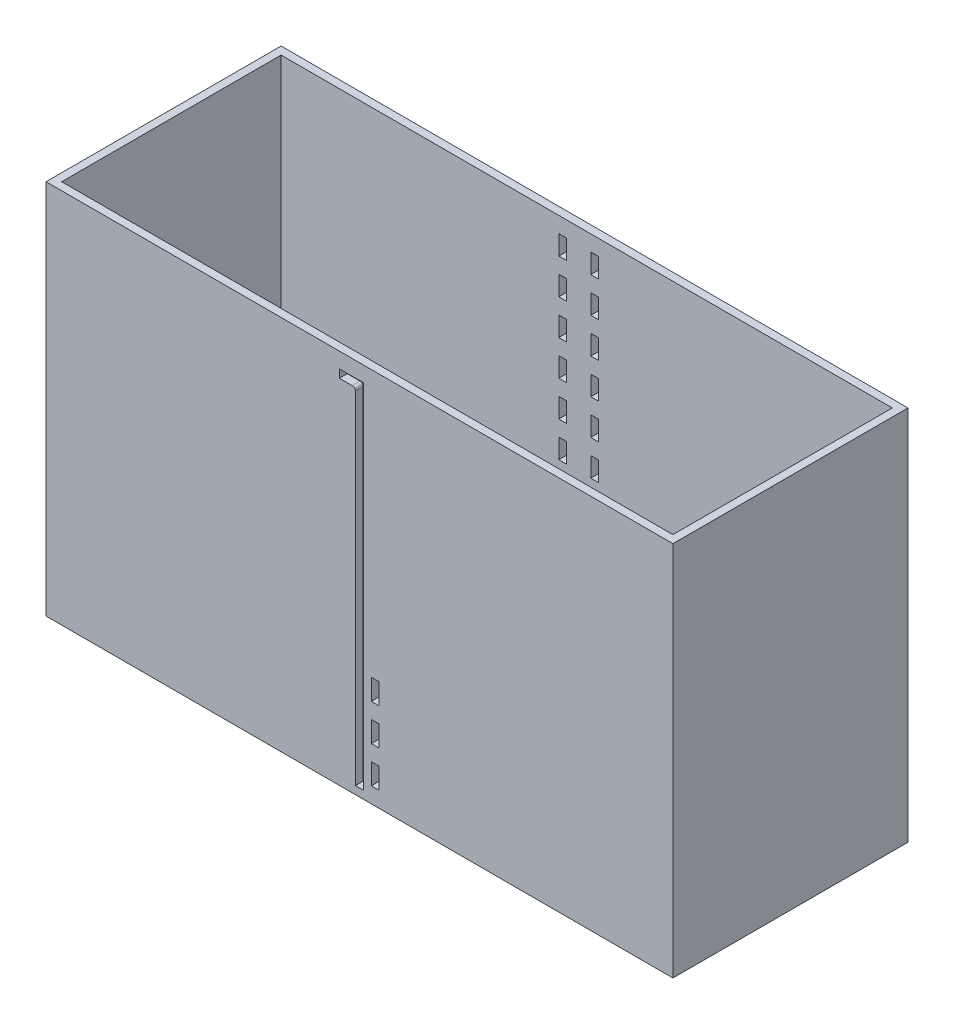
SolidWorks part; units mm, degrees
material "Acrylic (Medium-high impact)"
ref_plane "Front Plane" through (0, 0, 0) normal (0, 0, 1) x (1, 0, 0)
ref_plane "Top Plane" through (0, 0, 0) normal (0, 1, 0) x (1, 0, 0)
ref_plane "Right Plane" through (0, 0, 0) normal (1, 0, 0) x (0, 0, -1)
sketch "Sketch1" plane through (0, 0, 0) normal (0, 1, 0) x (1, 0, 0)
  line L1 (-254, 95.25) -> (254, 95.25)
  line L2 (-254, 95.25) -> (-254, -95.25)
  line L3 (-254, -95.25) -> (254, -95.25)
  line L4 (254, 95.25) -> (254, -95.25)
  point P4 (-254, 0)
  point P6 (0, 95.25)
  dimension "D1" = 190.5
  dimension "D2" = 508
extrude "Boss-Extrude1" add sketch "Sketch1" along normal blind 6.35
sketch "Sketch2" plane through (0, 6.35, 0) normal (0, 1, 0) x (1, 0, 0)
  line L0 (254, -95.25) -> (254, 95.25) construction
  line L1 (-254, 95.25) -> (254, 95.25)
  line L2 (-254, 95.25) -> (-254, -95.25)
  line L3 (-254, -95.25) -> (254, -95.25)
  line L4 (254, 95.25) -> (254, -95.25)
  line L5 (-254, -95.25) -> (254, -95.25) construction
  line L7 (-247.65, 88.9) -> (247.65, 88.9)
  line L8 (-247.65, 88.9) -> (-247.65, -88.9)
  line L9 (-247.65, -88.9) -> (247.65, -88.9)
  line L10 (247.65, 88.9) -> (247.65, -88.9)
  point P7 (-247.65, 0)
  point P14 (-254, 0)
  point P15 (0, -88.9)
  point P16 (0, -95.25)
  point P17 (247.65, 0)
  point P18 (254, 0)
  dimension "D1" = 6.35
  dimension "D2" = 6.35
extrude "Boss-Extrude2" add sketch "Sketch2" along normal blind 298.45
sketch "Sketch3" plane through (0, 0, 95.25) normal (0, 0, 1) x (1, 0, 0)
  line L0 (0, 304.8) -> (0, 0) construction
  line L1 (-254, 304.8) -> (254, 304.8) construction
  line L2 (-247.65, 6.35) -> (247.65, 6.35) construction
  line L4 (-3.302, 283.21) -> (-3.302, 6.35)
  line L5 (-3.302, 6.35) -> (3.302, 6.35)
  line L6 (3.302, 292.354) -> (3.302, 6.35)
  line L7 (3.302, 292.354) -> (-16.256, 292.354)
  line L9 (-5.842, 285.75) -> (-16.256, 285.75)
  line L10 (-16.256, 292.354) -> (-16.256, 285.75)
  line L11 (3.302, 101.6) -> (16.002, 101.6) construction
  line L12 (-254, 0) -> (254, 0) construction
  line L13 (12.827, 88.9) -> (12.827, 101.6) construction
  line L14 (9.652, 88.9) -> (16.002, 88.9)
  line L15 (9.652, 88.9) -> (9.652, 71.9667)
  line L16 (9.652, 71.9667) -> (16.002, 71.9667)
  line L17 (16.002, 88.9) -> (16.002, 71.9667)
  line L18 (9.652, 42.3333) -> (16.002, 42.3333)
  line L19 (9.652, 42.3333) -> (9.652, 59.2667)
  line L20 (9.652, 59.2667) -> (16.002, 59.2667)
  line L21 (16.002, 42.3333) -> (16.002, 59.2667)
  line L26 (9.652, 29.6333) -> (16.002, 29.6333)
  line L27 (9.652, 29.6333) -> (9.652, 12.7)
  line L28 (9.652, 12.7) -> (16.002, 12.7)
  line L29 (16.002, 29.6333) -> (16.002, 12.7)
  line L30 (12.827, 59.2667) -> (12.827, 71.9667) construction
  line L31 (12.827, 29.6333) -> (12.827, 42.3333) construction
  line L32 (12.827, 12.7) -> (12.827, 0) construction
  arc A0 (-3.302, 283.21) -> (-5.842, 285.75) centre (-5.842, 283.21) ccw
  point P5 (0, 6.35)
  dimension "D5" = 2.54
  dimension "D1" = 6.604
  dimension "D2" = 12.954
  dimension "D3" = 6.604
  dimension "D4" = 286.004
  dimension "D6" = 101.6
  dimension "D7" = 12.7
  dimension "D8" = 12.7
  dimension "D9" = 6.35
extrude "Cut-Extrude1" cut sketch "Sketch3" against normal blind 12.7
sketch "Sketch4" plane through (0, 0, -88.9) normal (0, 0, 1) x (1, 0, 0)
  line L0 (-254, 304.8) -> (254, 304.8) construction
  line L1 (-22.606, 304.8) -> (-16.256, 304.8)
  line L2 (-22.606, 304.8) -> (-22.606, 6.35)
  line L3 (-22.606, 6.35) -> (-16.256, 6.35)
  line L4 (-16.256, 304.8) -> (-16.256, 6.35)
  line L5 (6.477, 263.525) -> (6.477, 247.65) construction
  line L6 (-16.256, 292.354) -> (-16.256, 285.75) construction
  line L7 (3.302, 304.8) -> (9.652, 304.8)
  line L8 (3.302, 304.8) -> (3.302, 6.35)
  line L9 (3.302, 6.35) -> (9.652, 6.35)
  line L10 (9.652, 304.8) -> (9.652, 6.35)
  line L11 (247.65, 6.35) -> (-247.65, 6.35) construction
  line L12 (3.302, 6.35) -> (3.302, 292.354) construction
  line L13 (-16.256, 304.8) -> (-22.606, 304.8)
  line L14 (-16.256, 304.8) -> (-16.256, 292.1)
  line L15 (-16.256, 292.1) -> (-22.606, 292.1)
  line L16 (-22.606, 304.8) -> (-22.606, 292.1)
  line L17 (-16.256, 276.225) -> (-22.606, 276.225)
  line L18 (-16.256, 276.225) -> (-16.256, 263.525)
  line L19 (-16.256, 263.525) -> (-22.606, 263.525)
  line L20 (-22.606, 276.225) -> (-22.606, 263.525)
  line L21 (-22.606, 6.35) -> (-16.256, 6.35)
  line L22 (-22.606, 6.35) -> (-22.606, 19.05)
  line L23 (-22.606, 19.05) -> (-16.256, 19.05)
  line L24 (-16.256, 6.35) -> (-16.256, 19.05)
  line L25 (-22.606, 34.925) -> (-16.256, 34.925)
  line L26 (-22.606, 34.925) -> (-22.606, 47.625)
  line L27 (-22.606, 47.625) -> (-16.256, 47.625)
  line L28 (-16.256, 34.925) -> (-16.256, 47.625)
  line L29 (-22.606, 92.075) -> (-16.256, 92.075)
  line L30 (-22.606, 92.075) -> (-22.606, 104.775)
  line L31 (-22.606, 104.775) -> (-16.256, 104.775)
  line L32 (-16.256, 92.075) -> (-16.256, 104.775)
  line L33 (-22.606, 149.225) -> (-16.256, 149.225)
  line L34 (-22.606, 149.225) -> (-22.606, 161.925)
  line L35 (-22.606, 161.925) -> (-16.256, 161.925)
  line L36 (-16.256, 149.225) -> (-16.256, 161.925)
  line L37 (-22.606, 177.8) -> (-16.256, 177.8)
  line L38 (-22.606, 177.8) -> (-22.606, 190.5)
  line L39 (-22.606, 190.5) -> (-16.256, 190.5)
  line L40 (-16.256, 177.8) -> (-16.256, 190.5)
  line L41 (-22.606, 206.375) -> (-16.256, 206.375)
  line L42 (-22.606, 206.375) -> (-22.606, 219.075)
  line L43 (-22.606, 219.075) -> (-16.256, 219.075)
  line L44 (-16.256, 206.375) -> (-16.256, 219.075)
  line L45 (-22.606, 234.95) -> (-16.256, 234.95)
  line L46 (-22.606, 234.95) -> (-22.606, 247.65)
  line L47 (-22.606, 247.65) -> (-16.256, 247.65)
  line L48 (-16.256, 234.95) -> (-16.256, 247.65)
  line L49 (-16.256, 133.35) -> (-22.606, 133.35)
  line L50 (-16.256, 133.35) -> (-16.256, 120.65)
  line L51 (-16.256, 120.65) -> (-22.606, 120.65)
  line L52 (-22.606, 133.35) -> (-22.606, 120.65)
  line L53 (-16.256, 76.2) -> (-22.606, 76.2)
  line L54 (-16.256, 76.2) -> (-16.256, 63.5)
  line L55 (-16.256, 63.5) -> (-22.606, 63.5)
  line L56 (-22.606, 76.2) -> (-22.606, 63.5)
  line L57 (-19.431, 304.8) -> (-19.431, 292.1) construction
  line L58 (-19.431, 292.1) -> (-19.431, 276.225) construction
  line L59 (-19.431, 276.225) -> (-19.431, 263.525) construction
  line L60 (-19.431, 247.65) -> (-19.431, 234.95) construction
  line L61 (-19.431, 234.95) -> (-19.431, 219.075) construction
  line L62 (-19.431, 219.075) -> (-19.431, 206.375) construction
  line L63 (-19.431, 206.375) -> (-19.431, 190.5) construction
  line L64 (-19.431, 190.5) -> (-19.431, 177.8) construction
  line L65 (-19.431, 177.8) -> (-19.431, 161.925) construction
  line L66 (-19.431, 161.925) -> (-19.431, 149.225) construction
  line L67 (-19.431, 133.35) -> (-19.431, 120.65) construction
  line L68 (-19.431, 120.65) -> (-19.431, 104.775) construction
  line L69 (-19.431, 104.775) -> (-19.431, 92.075) construction
  line L70 (-19.431, 92.075) -> (-19.431, 76.2) construction
  line L71 (-19.431, 76.2) -> (-19.431, 63.5) construction
  line L72 (-19.431, 63.5) -> (-19.431, 47.625) construction
  line L73 (-19.431, 47.625) -> (-19.431, 34.925) construction
  line L74 (-19.431, 34.925) -> (-19.431, 19.05) construction
  line L75 (-19.431, 19.05) -> (-19.431, 6.35) construction
  line L76 (-19.431, 149.225) -> (-19.431, 133.35) construction
  line L77 (-19.431, 263.525) -> (-19.431, 247.65) construction
  line L78 (-6.477, 304.8) -> (-6.477, 0) construction
  line L79 (254, 304.8) -> (-254, 304.8) construction
  line L80 (254, 0) -> (-254, 0) construction
  line L81 (-6.477, 8.3493) -> (3.302, 8.3493) construction
  line L82 (-6.477, 8.3493) -> (-16.256, 8.3493) construction
  line L83 (6.477, 149.225) -> (6.477, 133.35) construction
  line L84 (6.477, 19.05) -> (6.477, 6.35) construction
  line L85 (6.477, 34.925) -> (6.477, 19.05) construction
  line L86 (6.477, 47.625) -> (6.477, 34.925) construction
  line L87 (6.477, 63.5) -> (6.477, 47.625) construction
  line L88 (6.477, 76.2) -> (6.477, 63.5) construction
  line L89 (6.477, 92.075) -> (6.477, 76.2) construction
  line L90 (6.477, 104.775) -> (6.477, 92.075) construction
  line L91 (6.477, 120.65) -> (6.477, 104.775) construction
  line L92 (6.477, 133.35) -> (6.477, 120.65) construction
  line L93 (6.477, 161.925) -> (6.477, 149.225) construction
  line L94 (6.477, 177.8) -> (6.477, 161.925) construction
  line L95 (6.477, 190.5) -> (6.477, 177.8) construction
  line L96 (6.477, 206.375) -> (6.477, 190.5) construction
  line L97 (6.477, 219.075) -> (6.477, 206.375) construction
  line L98 (6.477, 234.95) -> (6.477, 219.075) construction
  line L99 (6.477, 247.65) -> (6.477, 234.95) construction
  line L100 (6.477, 276.225) -> (6.477, 263.525) construction
  line L101 (6.477, 292.1) -> (6.477, 276.225) construction
  line L102 (6.477, 304.8) -> (6.477, 292.1) construction
  line L103 (9.652, 76.2) -> (9.652, 63.5)
  line L104 (3.302, 63.5) -> (9.652, 63.5)
  line L105 (3.302, 76.2) -> (3.302, 63.5)
  line L106 (3.302, 76.2) -> (9.652, 76.2)
  line L107 (9.652, 133.35) -> (9.652, 120.65)
  line L108 (3.302, 120.65) -> (9.652, 120.65)
  line L109 (3.302, 133.35) -> (3.302, 120.65)
  line L110 (3.302, 133.35) -> (9.652, 133.35)
  line L111 (3.302, 234.95) -> (3.302, 247.65)
  line L112 (9.652, 247.65) -> (3.302, 247.65)
  line L113 (9.652, 234.95) -> (9.652, 247.65)
  line L114 (9.652, 234.95) -> (3.302, 234.95)
  line L115 (3.302, 206.375) -> (3.302, 219.075)
  line L116 (9.652, 219.075) -> (3.302, 219.075)
  line L117 (9.652, 206.375) -> (9.652, 219.075)
  line L118 (9.652, 206.375) -> (3.302, 206.375)
  line L119 (3.302, 177.8) -> (3.302, 190.5)
  line L120 (9.652, 190.5) -> (3.302, 190.5)
  line L121 (9.652, 177.8) -> (9.652, 190.5)
  line L122 (9.652, 177.8) -> (3.302, 177.8)
  line L123 (3.302, 149.225) -> (3.302, 161.925)
  line L124 (9.652, 161.925) -> (3.302, 161.925)
  line L125 (9.652, 149.225) -> (9.652, 161.925)
  line L126 (9.652, 149.225) -> (3.302, 149.225)
  line L127 (3.302, 92.075) -> (3.302, 104.775)
  line L128 (9.652, 104.775) -> (3.302, 104.775)
  line L129 (9.652, 92.075) -> (9.652, 104.775)
  line L130 (9.652, 92.075) -> (3.302, 92.075)
  line L131 (3.302, 34.925) -> (3.302, 47.625)
  line L132 (9.652, 47.625) -> (3.302, 47.625)
  line L133 (9.652, 34.925) -> (9.652, 47.625)
  line L134 (9.652, 34.925) -> (3.302, 34.925)
  line L135 (3.302, 6.35) -> (3.302, 19.05)
  line L136 (9.652, 19.05) -> (3.302, 19.05)
  line L137 (9.652, 6.35) -> (9.652, 19.05)
  line L138 (9.652, 6.35) -> (3.302, 6.35)
  line L139 (9.652, 276.225) -> (9.652, 263.525)
  line L140 (3.302, 263.525) -> (9.652, 263.525)
  line L141 (3.302, 276.225) -> (3.302, 263.525)
  line L142 (3.302, 276.225) -> (9.652, 276.225)
  line L143 (9.652, 304.8) -> (9.652, 292.1)
  line L144 (3.302, 292.1) -> (9.652, 292.1)
  line L145 (3.302, 304.8) -> (3.302, 292.1)
  line L146 (3.302, 304.8) -> (9.652, 304.8)
  line L147 (3.302, 304.8) -> (3.302, 6.35)
  line L148 (9.652, 6.35) -> (3.302, 6.35)
  line L149 (9.652, 304.8) -> (9.652, 6.35)
  line L150 (9.652, 304.8) -> (3.302, 304.8)
  point P14 (-16.256, 289.052)
  dimension "D1" = 6.35
  dimension "D2" = 12.7
extrude "Cut-Extrude2" cut sketch "Sketch4" against normal up to next (6.35 mm away) contours L17 L4 L15 L2 | L2 L47 L4 L19 | L45 L2 L43 L4 | L41 L2 L39 L4 | L37 L2 L35 L4 | L49 L4 L33 L2 | L4 L51 L2 L31 | L53 L4 L29 L2 | L4 L55 L2 L27 | L25 L2 L23 L4
ref_plane "Plane1" through (-6.477, 0, 0) normal (-1, 0, 0) x (0, 0, 1)
mirror "Mirror1" about plane through (-6.477, 0, 0) normal (-1, 0, 0) of "Cut-Extrude2"
sketch "Sketch5" plane through (0, 0, 0) normal (0, -1, 0) x (-1, 0, 0)
  line L0 (-227.9316, -95.25) -> (-227.9316, -88.9)
  line L1 (-247.65, 88.9) -> (247.65, 88.9)
  line L2 (-247.65, 88.9) -> (-247.65, -88.9)
  line L3 (-247.65, -88.9) -> (247.65, -88.9)
  line L4 (247.65, 88.9) -> (247.65, -88.9)
  line L5 (-254, -95.25) -> (-241.3, -95.25)
  line L6 (-254, -95.25) -> (-254, -88.9)
  line L7 (-254, -88.9) -> (-241.3, -88.9)
  line L8 (-241.3, -95.25) -> (-241.3, -88.9)
  line L9 (-227.9316, -95.25) -> (-215.2316, -95.25)
  line L10 (-227.9316, -88.9) -> (-215.2316, -88.9)
  line L11 (-215.2316, -95.25) -> (-215.2316, -88.9)
  line L12 (-201.8632, -95.25) -> (-201.8632, -88.9)
  line L13 (-201.8632, -95.25) -> (-189.1632, -95.25)
  line L14 (-201.8632, -88.9) -> (-189.1632, -88.9)
  line L15 (-189.1632, -95.25) -> (-189.1632, -88.9)
  line L16 (-175.7947, -95.25) -> (-175.7947, -88.9)
  line L17 (-175.7947, -95.25) -> (-163.0947, -95.25)
  line L18 (-175.7947, -88.9) -> (-163.0947, -88.9)
  line L19 (-163.0947, -95.25) -> (-163.0947, -88.9)
  line L20 (-149.7263, -95.25) -> (-149.7263, -88.9)
  line L21 (-149.7263, -95.25) -> (-137.0263, -95.25)
  line L22 (-149.7263, -88.9) -> (-137.0263, -88.9)
  line L23 (-137.0263, -95.25) -> (-137.0263, -88.9)
  line L24 (-123.6579, -95.25) -> (-123.6579, -88.9)
  line L25 (-123.6579, -95.25) -> (-110.9579, -95.25)
  line L26 (-123.6579, -88.9) -> (-110.9579, -88.9)
  line L27 (-110.9579, -95.25) -> (-110.9579, -88.9)
  line L28 (-97.5895, -95.25) -> (-97.5895, -88.9)
  line L29 (-97.5895, -95.25) -> (-84.8895, -95.25)
  line L30 (-97.5895, -88.9) -> (-84.8895, -88.9)
  line L31 (-84.8895, -95.25) -> (-84.8895, -88.9)
  line L32 (-71.5211, -95.25) -> (-71.5211, -88.9)
  line L33 (-71.5211, -95.25) -> (-58.8211, -95.25)
  line L34 (-71.5211, -88.9) -> (-58.8211, -88.9)
  line L35 (-58.8211, -95.25) -> (-58.8211, -88.9)
  line L36 (-45.4526, -95.25) -> (-45.4526, -88.9)
  line L37 (-45.4526, -95.25) -> (-32.7526, -95.25)
  line L38 (-45.4526, -88.9) -> (-32.7526, -88.9)
  line L39 (-32.7526, -95.25) -> (-32.7526, -88.9)
  line L40 (-19.3842, -95.25) -> (-19.3842, -88.9)
  line L41 (-19.3842, -95.25) -> (-6.6842, -95.25)
  line L42 (-19.3842, -88.9) -> (-6.6842, -88.9)
  line L43 (-6.6842, -95.25) -> (-6.6842, -88.9)
  line L44 (6.6842, -95.25) -> (6.6842, -88.9)
  line L45 (6.6842, -95.25) -> (19.3842, -95.25)
  line L46 (6.6842, -88.9) -> (19.3842, -88.9)
  line L47 (19.3842, -95.25) -> (19.3842, -88.9)
  line L48 (32.7526, -95.25) -> (32.7526, -88.9)
  line L49 (32.7526, -95.25) -> (45.4526, -95.25)
  line L50 (32.7526, -88.9) -> (45.4526, -88.9)
  line L51 (45.4526, -95.25) -> (45.4526, -88.9)
  line L52 (58.8211, -95.25) -> (58.8211, -88.9)
  line L53 (58.8211, -95.25) -> (71.5211, -95.25)
  line L54 (58.8211, -88.9) -> (71.5211, -88.9)
  line L55 (71.5211, -95.25) -> (71.5211, -88.9)
  line L56 (84.8895, -95.25) -> (84.8895, -88.9)
  line L57 (84.8895, -95.25) -> (97.5895, -95.25)
  line L58 (84.8895, -88.9) -> (97.5895, -88.9)
  line L59 (97.5895, -95.25) -> (97.5895, -88.9)
  line L60 (110.9579, -95.25) -> (110.9579, -88.9)
  line L61 (110.9579, -95.25) -> (123.6579, -95.25)
  line L62 (110.9579, -88.9) -> (123.6579, -88.9)
  line L63 (123.6579, -95.25) -> (123.6579, -88.9)
  line L64 (137.0263, -95.25) -> (137.0263, -88.9)
  line L65 (137.0263, -95.25) -> (149.7263, -95.25)
  line L66 (137.0263, -88.9) -> (149.7263, -88.9)
  line L67 (149.7263, -95.25) -> (149.7263, -88.9)
  line L68 (163.0947, -95.25) -> (163.0947, -88.9)
  line L69 (163.0947, -95.25) -> (175.7947, -95.25)
  line L70 (163.0947, -88.9) -> (175.7947, -88.9)
  line L71 (175.7947, -95.25) -> (175.7947, -88.9)
  line L72 (189.1632, -95.25) -> (189.1632, -88.9)
  line L73 (189.1632, -95.25) -> (201.8632, -95.25)
  line L74 (189.1632, -88.9) -> (201.8632, -88.9)
  line L75 (201.8632, -95.25) -> (201.8632, -88.9)
  line L76 (215.2316, -95.25) -> (215.2316, -88.9)
  line L77 (215.2316, -95.25) -> (227.9316, -95.25)
  line L78 (215.2316, -88.9) -> (227.9316, -88.9)
  line L79 (227.9316, -95.25) -> (227.9316, -88.9)
  line L80 (241.3, -95.25) -> (241.3, -88.9)
  line L81 (241.3, -95.25) -> (254, -95.25)
  line L82 (241.3, -88.9) -> (254, -88.9)
  line L83 (254, -95.25) -> (254, -88.9)
  line L84 (-167.64, 0) -> (167.64, 0) construction
  line L85 (254, 95.25) -> (254, 88.9)
  line L86 (241.3, 88.9) -> (254, 88.9)
  line L87 (241.3, 95.25) -> (254, 95.25)
  line L88 (241.3, 95.25) -> (241.3, 88.9)
  line L89 (227.9316, 95.25) -> (227.9316, 88.9)
  line L90 (215.2316, 88.9) -> (227.9316, 88.9)
  line L91 (215.2316, 95.25) -> (227.9316, 95.25)
  line L92 (215.2316, 95.25) -> (215.2316, 88.9)
  line L93 (201.8632, 95.25) -> (201.8632, 88.9)
  line L94 (189.1632, 88.9) -> (201.8632, 88.9)
  line L95 (189.1632, 95.25) -> (201.8632, 95.25)
  line L96 (189.1632, 95.25) -> (189.1632, 88.9)
  line L97 (175.7947, 95.25) -> (175.7947, 88.9)
  line L98 (163.0947, 88.9) -> (175.7947, 88.9)
  line L99 (163.0947, 95.25) -> (175.7947, 95.25)
  line L100 (163.0947, 95.25) -> (163.0947, 88.9)
  line L101 (149.7263, 95.25) -> (149.7263, 88.9)
  line L102 (137.0263, 88.9) -> (149.7263, 88.9)
  line L103 (137.0263, 95.25) -> (149.7263, 95.25)
  line L104 (137.0263, 95.25) -> (137.0263, 88.9)
  line L105 (123.6579, 95.25) -> (123.6579, 88.9)
  line L106 (110.9579, 88.9) -> (123.6579, 88.9)
  line L107 (110.9579, 95.25) -> (123.6579, 95.25)
  line L108 (110.9579, 95.25) -> (110.9579, 88.9)
  line L109 (97.5895, 95.25) -> (97.5895, 88.9)
  line L110 (84.8895, 88.9) -> (97.5895, 88.9)
  line L111 (84.8895, 95.25) -> (97.5895, 95.25)
  line L112 (84.8895, 95.25) -> (84.8895, 88.9)
  line L113 (71.5211, 95.25) -> (71.5211, 88.9)
  line L114 (58.8211, 88.9) -> (71.5211, 88.9)
  line L115 (58.8211, 95.25) -> (71.5211, 95.25)
  line L116 (58.8211, 95.25) -> (58.8211, 88.9)
  line L117 (45.4526, 95.25) -> (45.4526, 88.9)
  line L118 (32.7526, 88.9) -> (45.4526, 88.9)
  line L119 (32.7526, 95.25) -> (45.4526, 95.25)
  line L120 (32.7526, 95.25) -> (32.7526, 88.9)
  line L121 (19.3842, 95.25) -> (19.3842, 88.9)
  line L122 (6.6842, 88.9) -> (19.3842, 88.9)
  line L123 (6.6842, 95.25) -> (19.3842, 95.25)
  line L124 (6.6842, 95.25) -> (6.6842, 88.9)
  line L125 (-6.6842, 95.25) -> (-6.6842, 88.9)
  line L126 (-19.3842, 88.9) -> (-6.6842, 88.9)
  line L127 (-19.3842, 95.25) -> (-6.6842, 95.25)
  line L128 (-19.3842, 95.25) -> (-19.3842, 88.9)
  line L129 (-32.7526, 95.25) -> (-32.7526, 88.9)
  line L130 (-45.4526, 88.9) -> (-32.7526, 88.9)
  line L131 (-45.4526, 95.25) -> (-32.7526, 95.25)
  line L132 (-45.4526, 95.25) -> (-45.4526, 88.9)
  line L133 (-58.8211, 95.25) -> (-58.8211, 88.9)
  line L134 (-71.5211, 88.9) -> (-58.8211, 88.9)
  line L135 (-71.5211, 95.25) -> (-58.8211, 95.25)
  line L136 (-71.5211, 95.25) -> (-71.5211, 88.9)
  line L137 (-84.8895, 95.25) -> (-84.8895, 88.9)
  line L138 (-97.5895, 88.9) -> (-84.8895, 88.9)
  line L139 (-97.5895, 95.25) -> (-84.8895, 95.25)
  line L140 (-97.5895, 95.25) -> (-97.5895, 88.9)
  line L141 (-110.9579, 95.25) -> (-110.9579, 88.9)
  line L142 (-123.6579, 88.9) -> (-110.9579, 88.9)
  line L143 (-123.6579, 95.25) -> (-110.9579, 95.25)
  line L144 (-123.6579, 95.25) -> (-123.6579, 88.9)
  line L145 (-137.0263, 95.25) -> (-137.0263, 88.9)
  line L146 (-149.7263, 88.9) -> (-137.0263, 88.9)
  line L147 (-149.7263, 95.25) -> (-137.0263, 95.25)
  line L148 (-149.7263, 95.25) -> (-149.7263, 88.9)
  line L149 (-163.0947, 95.25) -> (-163.0947, 88.9)
  line L150 (-175.7947, 88.9) -> (-163.0947, 88.9)
  line L151 (-175.7947, 95.25) -> (-163.0947, 95.25)
  line L152 (-175.7947, 95.25) -> (-175.7947, 88.9)
  line L153 (-189.1632, 95.25) -> (-189.1632, 88.9)
  line L154 (-201.8632, 88.9) -> (-189.1632, 88.9)
  line L155 (-201.8632, 95.25) -> (-189.1632, 95.25)
  line L156 (-201.8632, 95.25) -> (-201.8632, 88.9)
  line L157 (-215.2316, 95.25) -> (-215.2316, 88.9)
  line L158 (-227.9316, 88.9) -> (-215.2316, 88.9)
  line L159 (-227.9316, 95.25) -> (-215.2316, 95.25)
  line L160 (-241.3, 95.25) -> (-241.3, 88.9)
  line L161 (-254, 88.9) -> (-241.3, 88.9)
  line L162 (-254, 95.25) -> (-254, 88.9)
  line L163 (-254, 95.25) -> (-241.3, 95.25)
  line L164 (-247.65, 88.9) -> (247.65, 88.9)
  line L165 (-227.9316, 95.25) -> (-227.9316, 88.9)
  line L166 (-254, 65.6167) -> (-254, 52.9167)
  line L167 (-254, 95.25) -> (-247.65, 95.25)
  line L168 (-254, 95.25) -> (-254, 82.55)
  line L169 (-254, 82.55) -> (-247.65, 82.55)
  line L170 (-247.65, 95.25) -> (-247.65, 82.55)
  line L171 (-254, 65.6167) -> (-247.65, 65.6167)
  line L172 (-247.65, 65.6167) -> (-247.65, 52.9167)
  line L173 (-254, 52.9167) -> (-247.65, 52.9167)
  line L174 (-254, 35.9833) -> (-254, 23.2833)
  line L175 (-254, 35.9833) -> (-247.65, 35.9833)
  line L176 (-247.65, 35.9833) -> (-247.65, 23.2833)
  line L177 (-254, 23.2833) -> (-247.65, 23.2833)
  line L178 (-254, 6.35) -> (-254, -6.35)
  line L179 (-254, 6.35) -> (-247.65, 6.35)
  line L180 (-247.65, 6.35) -> (-247.65, -6.35)
  line L181 (-254, -6.35) -> (-247.65, -6.35)
  line L182 (-254, -23.2833) -> (-254, -35.9833)
  line L183 (-254, -23.2833) -> (-247.65, -23.2833)
  line L184 (-247.65, -23.2833) -> (-247.65, -35.9833)
  line L185 (-254, -35.9833) -> (-247.65, -35.9833)
  line L186 (-254, -52.9167) -> (-254, -65.6167)
  line L187 (-254, -52.9167) -> (-247.65, -52.9167)
  line L188 (-247.65, -52.9167) -> (-247.65, -65.6167)
  line L189 (-254, -65.6167) -> (-247.65, -65.6167)
  line L190 (-254, -82.55) -> (-254, -95.25)
  line L191 (-254, -82.55) -> (-247.65, -82.55)
  line L192 (-247.65, -82.55) -> (-247.65, -95.25)
  line L193 (-254, -95.25) -> (-247.65, -95.25)
  line L194 (0, 104.775) -> (0, -104.775) construction
  line L195 (254, -95.25) -> (247.65, -95.25)
  line L196 (247.65, -82.55) -> (247.65, -95.25)
  line L197 (254, -82.55) -> (247.65, -82.55)
  line L198 (254, -82.55) -> (254, -95.25)
  line L199 (254, -65.6167) -> (247.65, -65.6167)
  line L200 (247.65, -52.9167) -> (247.65, -65.6167)
  line L201 (254, -52.9167) -> (247.65, -52.9167)
  line L202 (254, -52.9167) -> (254, -65.6167)
  line L203 (254, -35.9833) -> (247.65, -35.9833)
  line L204 (247.65, -23.2833) -> (247.65, -35.9833)
  line L205 (254, -23.2833) -> (247.65, -23.2833)
  line L206 (254, -23.2833) -> (254, -35.9833)
  line L207 (254, -6.35) -> (247.65, -6.35)
  line L208 (247.65, 6.35) -> (247.65, -6.35)
  line L209 (254, 6.35) -> (247.65, 6.35)
  line L210 (254, 6.35) -> (254, -6.35)
  line L211 (254, 23.2833) -> (247.65, 23.2833)
  line L212 (247.65, 35.9833) -> (247.65, 23.2833)
  line L213 (254, 35.9833) -> (247.65, 35.9833)
  line L214 (254, 35.9833) -> (254, 23.2833)
  line L215 (254, 52.9167) -> (247.65, 52.9167)
  line L216 (247.65, 65.6167) -> (247.65, 52.9167)
  line L217 (254, 65.6167) -> (247.65, 65.6167)
  line L218 (247.65, 95.25) -> (247.65, 82.55)
  line L219 (254, 82.55) -> (247.65, 82.55)
  line L220 (254, 95.25) -> (254, 82.55)
  line L221 (254, 95.25) -> (247.65, 95.25)
  line L222 (254, 65.6167) -> (254, 52.9167)
  line L223 (254, 95.25) -> (254, 88.9)
  line L224 (254, -95.25) -> (254, -88.9)
  line L225 (247.65, 88.9) -> (247.65, -88.9)
  point P6 (0, 0)
  dimension "D1" = 12.7
  dimension "D3" = 6.35
  dimension "D5" = 12.7
  dimension "D2" = 20
  dimension "D4" = 7
